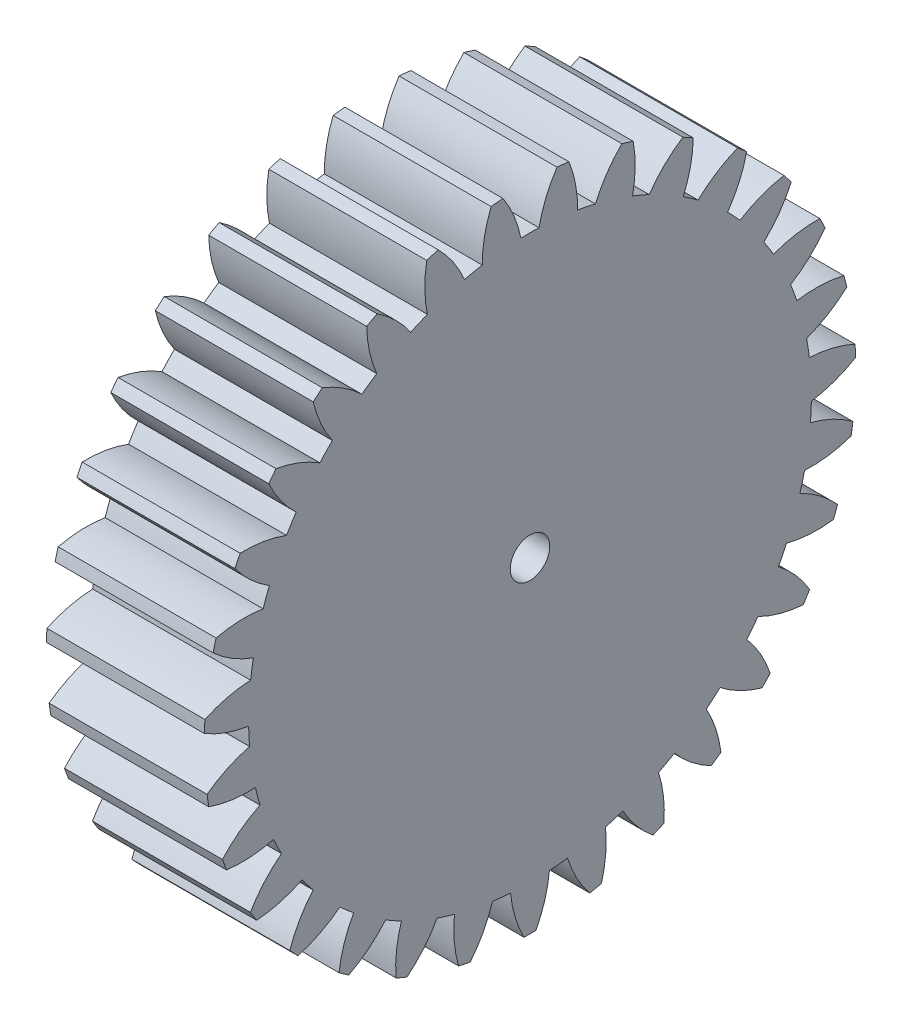
SolidWorks part; units mm, degrees
ref_plane "Plane1" through (0, 0, 0) normal (0, 0, 1) x (1, 0, 0)
ref_plane "Plane2" through (0, 0, 0) normal (0, 1, 0) x (1, 0, 0)
ref_plane "Plane3" through (0, 0, 0) normal (1, 0, 0) x (0, 0, -1)
sketch "HoldingSke" plane through (0, 0, 0) normal (0, 1, 0) x (1, 0, 0)
  line L0 (0, 0) -> (0.3429, -0.206)
  line L1 (-15, 0) -> (100, 0) construction
  line L2 (0, 0) -> (-2.1039, 2.3779)
  line L3 (0, 0) -> (-11.863, 4.5341)
  line L4 (0, 0) -> (7.4025, 4.4479)
  line L5 (0, 0) -> (-46.8476, -17.4728)
  line L6 (0, 0) -> (-16.5793, -11.1861)
  line L7 (-2.1039, 2.3779) -> (8.6586, 51.2059)
  line L8 (-76.2, 54.61) -> (-75.3, 54.61)
  line L9 (-71.009, 38.7566) -> (-53.1078, 45.2721)
  line L10 (-76.2, 71.12) -> (104.1128, 71.12)
  line L11 (0, 0) -> (-20, 0)
  line L12 (-76.2, 101.6) -> (-76.113, 101.6)
  line L13 (24.9733, 27.94) -> (52.9518, 28.4284)
  line L14 (24.9733, 27.94) -> (24.9743, 27.94)
  line L15 (24.9733, 27.94) -> (100.4006, 29.5858)
  line L16 (-63.627, -2.5) -> (-12.827, -2.5)
  circle A0 centre (0, 0) radius 2.5
  circle A1 centre (0, 0) radius 35.624
  circle A2 centre (0, 0) radius 37.5
  circle A3 centre (0, 0) radius 2.5
  dimension "MHD" = 71.248
  dimension "Hub_dia" = 75
  dimension "Bore" = 5
  dimension "MBD" = 5
  dimension "Num_teeth" = 31
  dimension "Pitch" = 0.4
  dimension "Overall_len" = 50
  dimension "Show_teeth" = 31
  dimension "Thickness" = 20
  dimension "OAL" = 50.0001
  dimension "T_dim" = 0.9
  dimension "Ap" = 20
  dimension "H" = 19.05
  dimension "Pitch_radius" = 180.3128
  dimension "Width" = 20
  dimension "Backlash" = 0.087
  dimension "Addendum_fac" = 1
  dimension "Dedendum_fac" = 1.25
  dimension "Clearance_fac" = 0.25
  dimension "Dedendum_add" = 0.001
  dimension "Module" = 2.5
sketch "BasProSke" plane through (0, 0, 0) normal (0, 1, 0) x (1, 0, 0)
  line L0 (-10, 0) -> (60, 0) construction
  line L1 (0, 0) -> (0, 41.25)
  line L2 (0, 0) -> (20, 0)
  line L3 (20, 0) -> (20, 41.25)
  line L4 (20, 41.25) -> (0, 41.25)
  dimension "Thickness" = 20
  dimension "Diameter" = 82.5
revolve "Base-Revolve" add sketch "BasProSke" angle 360 about L0
sketch "TooCutSke" plane through (0, 0, 0) normal (1, 0, 0) x (0, 0, -1)
  line L1 (0, 0) -> (0, 107) construction
  line L2 (0, 0) -> (-2.1149, 38.6922) construction
  line L3 (0, 0) -> (-7.832, 77.0182) construction
  line L4 (-2.1149, 38.6922) -> (-3.916, 38.5091) construction
  arc A0 (1.1478, 35.6055) -> (-1.1478, 35.6055) centre (0, 0) ccw
  arc A1 (3.4407, 41.1317) -> (-3.4407, 41.1317) centre (0, 0) ccw
  circle A2 centre (0, 0) radius 38.75 construction
  circle A3 centre (0, 0) radius 36.4131 construction
  arc A4 (-1.1478, 35.6055) -> (-3.4407, 41.1317) centre (-16.3417, 32.5402) ccw
  arc A5 (3.4407, 41.1317) -> (1.1478, 35.6055) centre (16.3417, 32.5402) ccw
  dimension "Root_dia" = 71.248
  dimension "Overcut_dia" = 82.5508
  dimension "Pitch_dia" = 77.5
  dimension "Base_dia" = 72.8262
  dimension "Flank_rad" = 15.5
  dimension "Half_ang" = 5.806
  dimension "Half_CT" = 1.8104
extrude "ToothCut" cut sketch "TooCutSke" along normal through all
fillet "Breaks" [suppressed] radius 0.05
fillet "RootFillets" [suppressed] radius 0.626
pattern_circular "TeethCuts" count 31 every 11.613 about axis through (-10, 0, 0) along (1, 0, 0) of "ToothCut", "RootFillets", "Breaks"
sketch "HubNeaOneSke" plane through (0, 0, 0) normal (-1, 0, 0) x (0, 0, 1)
  circle A0 centre (0, 0) radius 35.624
  dimension "Diameter" = 71.248
extrude "HubNearOne" [suppressed] add sketch "HubNeaOneSke" along normal blind 30.0001
sketch "HubNeaBotSke" plane through (0, 0, 0) normal (-1, 0, 0) x (0, 0, 1)
  circle A0 centre (0, 0) radius 35.624
  dimension "Diameter" = 71.248
extrude "HubNearBoth" [suppressed] add sketch "HubNeaBotSke" along normal blind 15
ref_plane "FarPln" through (20, 0, 0) normal (1, 0, 0) x (0, 0, -1)
sketch "HubFarSke" plane through (20, 0, 0) normal (1, 0, 0) x (0, 0, -1)
  circle A0 centre (0, 0) radius 35.624
  dimension "Diameter" = 71.248
extrude "HubFar" [suppressed] add sketch "HubFarSke" along normal blind 15
sketch "BorSke" plane through (0, 0, 0) normal (1, 0, 0) x (0, 0, -1)
  circle A0 centre (0, 0) radius 2.5
  dimension "Diameter" = 5
extrude "Bore" cut sketch "BorSke" along normal mid plane 100.0001
sketch "KeySke" plane through (0, 0, 0) normal (1, 0, 0) x (0, 0, -1)
  line L0 (-1, 0) -> (-1, 3.4)
  line L1 (-1, 3.4) -> (1, 3.4)
  line L2 (1, 3.4) -> (1, 0)
  line L3 (0, 0) -> (0, 34) construction
  line L4 (-1, 0) -> (1, 0)
  dimension "Offset" = 3.4
extrude "Keyway" [suppressed] cut sketch "KeySke" along normal mid plane 100.0001
pattern_circular "Keyway2" [suppressed] count 2 every 90 about axis through (-10, 0, 0) along (1, 0, 0)
equation "' \"Module@HoldingSke\" = 6.35"
equation "' \"Num_teeth@HoldingSke\" = 12"
equation "' \"Ap@HoldingSke\" =  20"
equation "' \"Ap@HoldingSke\" = 20"
equation "' \"Width@HoldingSke\" = 0.5 * 25.4"
equation "' \"Hub_dia@HoldingSke\"= 1 * 25.4"
equation "' \"Hub_dia@HoldingSke\" = 1 * 25.4"
equation "' \"Overall_len@HoldingSke\" = 1.0 * 25.4"
equation "' \"Bore@HoldingSke\" = 0.75 * 25.4"
equation "' \"T_dim@HoldingSke\" = 0.1 * 25.4"
equation "' \"Width@KeySke\" = 0.25 * 25.4"
equation "' \"Show_teeth@HoldingSke\" = 13"
equation "' \"Backlash@HoldingSke\" = 0.009 * 25.4"
equation "' \"Addendum_fac@HoldingSke\" = 1.0"
equation "' \"Dedendum_fac@HoldingSke\" = 1.25"
equation "' \"Dedendum_add@HoldingSke\" = 0.00005 * 25.4"
equation "' \"Clearance_fac@HoldingSke\" = 0.25"
equation "\"Pitch@HoldingSke\" = 1 / \"Module@HoldingSke\""
equation "\"Overcut_dia@TooCutSke\" = (\"Num_teeth@HoldingSke\" + 2 * \"Addendum_fac@HoldingSke\") / \"Pitch@HoldingSke\" + 0.002 * 25.4"
equation "\"Pitch_dia@TooCutSke\" = \"Num_teeth@HoldingSke\" / \"Pitch@HoldingSke\""
equation "\"Base_dia@TooCutSke\" = \"Num_teeth@HoldingSke\" / \"Pitch@HoldingSke\" * cos((\"Ap@HoldingSke\"  * 3.14159265 / 180))"
equation "\"Root_dia@TooCutSke\" = (\"Num_teeth@HoldingSke\" + 2) / \"Pitch@HoldingSke\" - 2 * (\"Addendum_fac@HoldingSke\" + \"Dedendum_fac@HoldingSke\") / \"Pitch@HoldingSke\" - \"Dedendum_add@HoldingSke\" * 2"
equation "\"Half_ang@TooCutSke\" = 180 / \"Num_teeth@HoldingSke\""
equation "\"Half_CT@TooCutSke\" = \"Num_teeth@HoldingSke\" / \"Pitch@HoldingSke\" * sin((3.14159265 / 2 / \"Num_teeth@HoldingSke\")) / 2 - 7 * \"Backlash@HoldingSke\" / 4"
equation "\"Flank_rad@TooCutSke\" = \"Num_teeth@HoldingSke\" / \"Pitch@HoldingSke\" / 5"
equation "\"Radius@RootFillets\" = \"Clearance_fac@HoldingSke\" / \"Pitch@HoldingSke\" + \"Dedendum_add@HoldingSke\""
equation "\"Break_rad@Breaks\" = 0.02 / \"Pitch@HoldingSke\""
equation "\"Thickness@HoldingSke\" = \"Width@HoldingSke\""
equation "\"OAL@HoldingSke\" = \"Thickness@HoldingSke\""
equation "\"MHD@HoldingSke\" = (\"Num_teeth@HoldingSke\" + 2) / \"Pitch@HoldingSke\" - 2 * (\"Addendum_fac@HoldingSke\" + \"Dedendum_fac@HoldingSke\")  / \"Pitch@HoldingSke\" - \"Dedendum_add@HoldingSke\" * 2"
equation "\"MBD@HoldingSke\" = (\"Num_teeth@HoldingSke\" + 2) / \"Pitch@HoldingSke\" - 2 * (\"Addendum_fac@HoldingSke\" + \"Dedendum_fac@HoldingSke\")  / \"Pitch@HoldingSke\" - \"Dedendum_add@HoldingSke\" * 2 - 0.002 * 25.4"
equation "\"MHD@HoldingSke\" = ((sgn( \"MHD@HoldingSke\" - \"Hub_dia@HoldingSke\" )-1)*( \"MHD@HoldingSke\" - \"Hub_dia@HoldingSke\" ))/-2+ \"Hub_dia@HoldingSke\""
equation "\"MBD@HoldingSke\" = ((sgn( \"MBD@HoldingSke\" - \"Bore@HoldingSke\" )-1)*( \"MBD@HoldingSke\" - \"Bore@HoldingSke\" ))/-2+ \"Bore@HoldingSke\""
equation "\"OAL@HoldingSke\" = ((sgn( \"OAL@HoldingSke\" - \"Overall_len@HoldingSke\" )+1)*( \"OAL@HoldingSke\" - \"Overall_len@HoldingSke\" ))/2 + \"Overall_len@HoldingSke\" + 0.000002 * 25.4"
equation "\"Num_teeth@TeethCuts\" = int( \"Show_teeth@HoldingSke\" ) + 1"
equation "\"Num_teeth@TeethCuts\" = ((sgn( \"Num_teeth@TeethCuts\" - \"Num_teeth@HoldingSke\" )-1)*( \"Num_teeth@TeethCuts\" - \"Num_teeth@HoldingSke\" ))/-2+ \"Num_teeth@HoldingSke\""
equation "\"Num_teeth@TeethCuts\" = ((sgn( \"Num_teeth@TeethCuts\" - 2.0)+1)*( \"Num_teeth@TeethCuts\" - 2.0))/2 +2.0"
equation "\"Angle@TeethCuts\" = 360.0 / \"Num_teeth@HoldingSke\""
equation "\"Diameter@BasProSke\" = (\"Num_teeth@HoldingSke\" + 2 * \"Addendum_fac@HoldingSke\") / \"Pitch@HoldingSke\""
equation "\"Thickness@BasProSke\"  = \"Thickness@HoldingSke\""
equation "' \"Fillet_rad@BasProSke\" =  \"Thickness@HoldingSke\" * 0.05"
equation "' \"Fillet_rad@BasProSke\" = \"Thickness@HoldingSke\" * 0.05"
equation "\"MHD@HoldingSke\" = ((sgn( \"MHD@HoldingSke\" - \"Root_dia@TooCutSke\" )-1)*( \"MHD@HoldingSke\" - \"Root_dia@TooCutSke\" ))/-2+ \"Root_dia@TooCutSke\""
equation "\"Diameter@HubNeaOneSke\" = \"MHD@HoldingSke\""
equation "\"Length@HubNearOne\" = \"OAL@HoldingSke\" - \"Thickness@BasProSke\""
equation "\"Diameter@HubNeaBotSke\" = \"MHD@HoldingSke\""
equation "\"Length@HubNearBoth\" = ( \"OAL@HoldingSke\" - \"Thickness@BasProSke\" ) / 2.0"
equation "\"Thickness@FarPln\" = \"Thickness@BasProSke\""
equation "\"Diameter@HubFarSke\" = \"MHD@HoldingSke\""
equation "\"Length@HubFar\" = ( \"OAL@HoldingSke\" - \"Thickness@BasProSke\" ) / 2.0"
equation "\"Diameter@BorSke\" = \"MBD@HoldingSke\""
equation "\"D1@Bore\" = \"OAL@HoldingSke\" * 2.0"
equation "\"D1@Keyway\" = \"OAL@HoldingSke\" * 2.0"
equation "\"Offset@KeySke\" = \"T_dim@HoldingSke\" + \"MBD@HoldingSke\" / 2.0"
